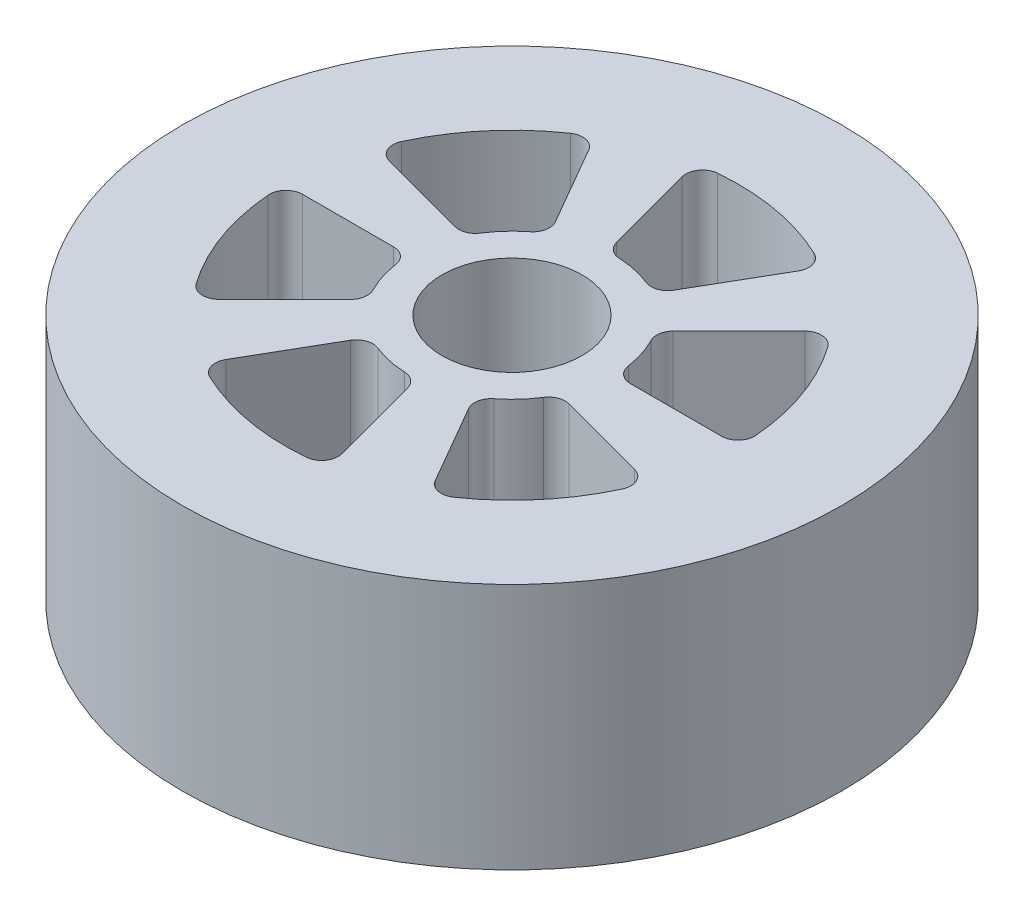
SolidWorks part; units mm, degrees
ref_plane "Front Plane" through (0, 0, 0) normal (0, 0, 1) x (1, 0, 0)
ref_plane "Top Plane" through (0, 0, 0) normal (0, 1, 0) x (1, 0, 0)
ref_plane "Right Plane" through (0, 0, 0) normal (1, 0, 0) x (0, 0, -1)
sketch "Sketch1" plane through (0, 0, 0) normal (0, 1, 0) x (1, 0, 0)
  line L0 (36.478, 0) -> (64.5705, 0)
  line L1 (29.0689, 20.6129) -> (49.3547, 40.8988)
  line L2 (32.3858, -14.8679) -> (60.0967, -22.293)
  line L3 (18.239, -31.5909) -> (32.2852, -55.9197)
  line L4 (3.3169, -35.4809) -> (10.742, -63.1918)
  line L5 (-18.239, -31.5909) -> (-32.2852, -55.9197)
  line L6 (-29.0689, -20.6129) -> (-49.3547, -40.8988)
  line L7 (-36.478, 0) -> (-64.5705, 0)
  line L8 (-32.3858, 14.8679) -> (-60.0967, 22.293)
  line L9 (-18.239, 31.5909) -> (-32.2852, 55.9197)
  line L10 (-3.3169, 35.4809) -> (-10.742, 63.1918)
  line L11 (18.239, 31.5909) -> (32.2852, 55.9197)
  circle A0 centre (0, 0) radius 101.6
  arc A2 (69.6348, 5.4784) -> (57.0995, 40.2327) centre (0, 0) ccw
  arc A3 (31.4465, 4.3793) -> (28.156, 14.6731) centre (0, 0) ccw
  arc A4 (31.4465, 4.3793) -> (36.478, 0) centre (36.478, 5.08) ccw
  arc A5 (29.0689, 20.6129) -> (28.156, 14.6731) centre (32.661, 17.0208) ccw
  arc A6 (57.0995, 40.2327) -> (49.3547, 40.8988) centre (52.9468, 37.3067) ccw
  arc A7 (69.6348, 5.4784) -> (64.5705, 0) centre (64.5705, 5.08) cw
  arc A8 (39.5619, -57.5663) -> (63.3923, -29.3333) centre (0, 0) ccw
  arc A9 (39.5619, -57.5663) -> (32.2852, -55.9197) centre (36.6846, -53.3797) cw
  arc A10 (63.3923, -29.3333) -> (60.0967, -22.293) centre (58.7819, -27.1999) ccw
  arc A11 (32.3858, -14.8679) -> (26.7853, -17.0473) centre (31.071, -19.7748) ccw
  arc A12 (19.5159, -25.0438) -> (26.7853, -17.0473) centre (0, 0) ccw
  arc A13 (19.5159, -25.0438) -> (18.239, -31.5909) centre (22.6384, -29.0509) ccw
  arc A14 (-30.073, -63.0447) -> (6.2928, -69.566) centre (0, 0) ccw
  arc A15 (-30.073, -63.0447) -> (-32.2852, -55.9197) centre (-27.8858, -58.4597) cw
  arc A16 (6.2928, -69.566) -> (10.742, -63.1918) centre (5.8351, -64.5066) ccw
  arc A17 (3.3169, -35.4809) -> (-1.3707, -31.7204) centre (-1.59, -36.7957) ccw
  arc A18 (-11.9307, -29.4231) -> (-1.3707, -31.7204) centre (0, 0) ccw
  arc A19 (-11.9307, -29.4231) -> (-18.239, -31.5909) centre (-13.8396, -34.1309) ccw
  arc A20 (-69.6348, -5.4784) -> (-57.0995, -40.2327) centre (0, 0) ccw
  arc A21 (-69.6348, -5.4784) -> (-64.5705, 0) centre (-64.5705, -5.08) cw
  arc A22 (-57.0995, -40.2327) -> (-49.3547, -40.8988) centre (-52.9468, -37.3067) ccw
  arc A23 (-29.0689, -20.6129) -> (-28.156, -14.6731) centre (-32.661, -17.0208) ccw
  arc A24 (-31.4465, -4.3793) -> (-28.156, -14.6731) centre (0, 0) ccw
  arc A25 (-31.4465, -4.3793) -> (-36.478, 0) centre (-36.478, -5.08) ccw
  arc A26 (-39.5619, 57.5663) -> (-63.3923, 29.3333) centre (0, 0) ccw
  arc A27 (-39.5619, 57.5663) -> (-32.2852, 55.9197) centre (-36.6846, 53.3797) cw
  arc A28 (-63.3923, 29.3333) -> (-60.0967, 22.293) centre (-58.7819, 27.1999) ccw
  arc A29 (-32.3858, 14.8679) -> (-26.7853, 17.0473) centre (-31.071, 19.7748) ccw
  arc A30 (-19.5159, 25.0438) -> (-26.7853, 17.0473) centre (0, 0) ccw
  arc A31 (-19.5159, 25.0438) -> (-18.239, 31.5909) centre (-22.6384, 29.0509) ccw
  arc A32 (30.073, 63.0447) -> (-6.2928, 69.566) centre (0, 0) ccw
  arc A33 (30.073, 63.0447) -> (32.2852, 55.9197) centre (27.8858, 58.4597) cw
  arc A34 (-6.2928, 69.566) -> (-10.742, 63.1918) centre (-5.8351, 64.5066) ccw
  arc A35 (-3.3169, 35.4809) -> (1.3707, 31.7204) centre (1.59, 36.7957) ccw
  arc A36 (11.9307, 29.4231) -> (1.3707, 31.7204) centre (0, 0) ccw
  arc A37 (11.9307, 29.4231) -> (18.239, 31.5909) centre (13.8396, 34.1309) ccw
  point P5 (31.75, 0)
  point P16 (69.85, 0)
  point P79 (0, 0)
  dimension "D1" = 203.2
  dimension "D2" = 5.08
  dimension "D3" = 139.7
  dimension "D4" = 63.5
  dimension "D5" = 45
  dimension "D6" = 6
extrude "Boss-Extrude2" add sketch "Sketch1" along normal blind 76.2
sketch "Sketch2" plane through (0, 76.2, 0) normal (0, 1, 0) x (1, 0, 0)
  circle A0 centre (0, 0) radius 21.59
  dimension "D1" = 43.18
extrude "Cut-Extrude1" cut sketch "Sketch2" against normal blind 76.2
